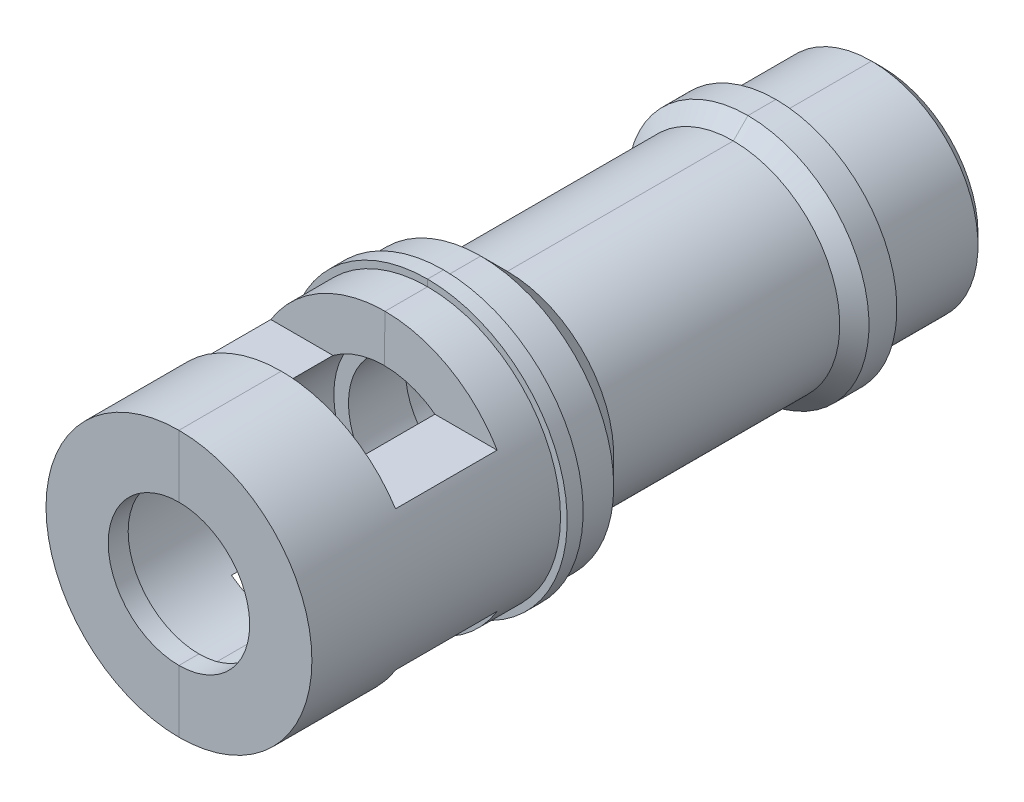
SolidWorks part; units mm, degrees
ref_plane "Спереди" through (0, 0, 0) normal (0, 0, 1) x (1, 0, 0)
ref_plane "Сверху" through (0, 0, 0) normal (0, 1, 0) x (1, 0, 0)
ref_plane "Справа" through (0, 0, 0) normal (1, 0, 0) x (0, 0, -1)
other "Configuration Table"
sketch "Sketch1" plane through (0, 0, 0) normal (1, 0, 0) x (0, 0, -1)
  line L1 (0, -10) -> (18.7, -10)
  line L3 (18.7, -10.5) -> (19.9, -10.5)
  line L5 (19.9, -10) -> (22.7, -10)
  line L6 (24.7, -8) -> (41.7, -8)
  line L7 (22.7, -10) -> (24.7, -8)
  line L10 (42.8, -9.1) -> (41.7, -8)
  line L11 (42.8, -9.1) -> (44.9, -9.1)
  line L12 (44.9192, -8) -> (52.1, -8)
  line L14 (52.9, -7.2) -> (52.9, -6.5)
  line L15 (52.9, 0) -> (0, 0) construction
  line L18 (44.9, -9.1) -> (44.9192, -8)
  line L19 (0, -5.3188) -> (0, -10)
  line L20 (1.5, -6.5) -> (18.1483, -6.5)
  line L21 (52.1, -8) -> (52.9, -7.2)
  line L22 (41.0965, -6.5) -> (41.0965, -5.5)
  line L23 (41.0965, -5.5) -> (39.0965, -5.5)
  line L24 (39.0965, -5.5) -> (39.0965, -6.5)
  line L25 (41.0965, -6.5) -> (52.9, -6.5)
  line L27 (0, -5.3188) -> (1.5, -5.3188)
  line L28 (1.5, -5.3188) -> (1.5, -6.5)
  line L29 (18.1483, -5.399) -> (22.4482, -5.4198)
  line L30 (22.4482, -5.4198) -> (22.4482, -6.5)
  line L31 (18.1483, -5.399) -> (18.1483, -6.5)
  line L32 (22.4482, -6.5) -> (39.0965, -6.5)
  line L34 (19.9, -10) -> (19.9, -10.5)
  line L37 (18.7, -10) -> (18.7, -10.5)
  point P14 (52.9, -8)
  point P15 (18.7, 12.0596)
  point P26 (18.7, -14.9587)
  point P30 (20.2982, -5.4094)
  point P31 (19.9, 12.0596)
  point P32 (19.9, -14.9587)
revolve "Revolve1" add sketch "Sketch1" angle 360 about L15
sketch "Sketch3" plane through (0, 0, 0) normal (1, 0, 0) x (0, 0, -1)
  line L2 (7.7808, -5.25) -> (7.5811, -16.6932)
  line L4 (7.5811, 16.6932) -> (15.6189, 16.6932)
  line L5 (15.4192, 5.25) -> (15.6189, 16.6932)
  line L6 (7.7808, 5.25) -> (7.5811, 16.6932)
  line L7 (15.4192, -5.25) -> (15.6189, -16.6932)
  line L8 (7.5811, -16.6932) -> (15.6189, -16.6932)
  line L10 (7.7808, 5.25) -> (15.4192, 5.25)
  line L11 (7.7808, -5.25) -> (15.4192, -5.25)
  point P13 (0, 0)
extrude "Cut-Extrude1" cut sketch "Sketch3" against normal through all both and the other way through all
sketch "Sketch4" plane through (0, 0, 0) normal (0, 0, 1) x (1, 0, 0)
  line L0 (-0.75, 6.5129) -> (-0.75, -6.4871) construction
  line L1 (0.75, -6.4871) -> (-0.75, -6.4871) construction
  line L2 (0.75, 6.5129) -> (0.75, -6.4871) construction
  line L3 (-0.95, 6.7129) -> (-0.95, -6.6871)
  line L4 (0.95, -6.6871) -> (-0.95, -6.6871)
  line L5 (0.75, 6.5129) -> (-0.75, 6.5129) construction
  line L6 (0.95, 6.7129) -> (0.95, -6.6871)
  line L7 (0.95, 6.7129) -> (-0.95, 6.7129)
  point P3 (0, 0)
  dimension "D1" = 0.2
extrude "Cut-Extrude2" cut sketch "Sketch4" along normal up to surface (11.8035 mm away) from surface at -52.9 up to face at (0, 5.5, -41.0965) starting at face at (0, 6.5, -52.9)
split "Split1" trim tools "Справа" bodies to split 107 resulting bodies 105 106
